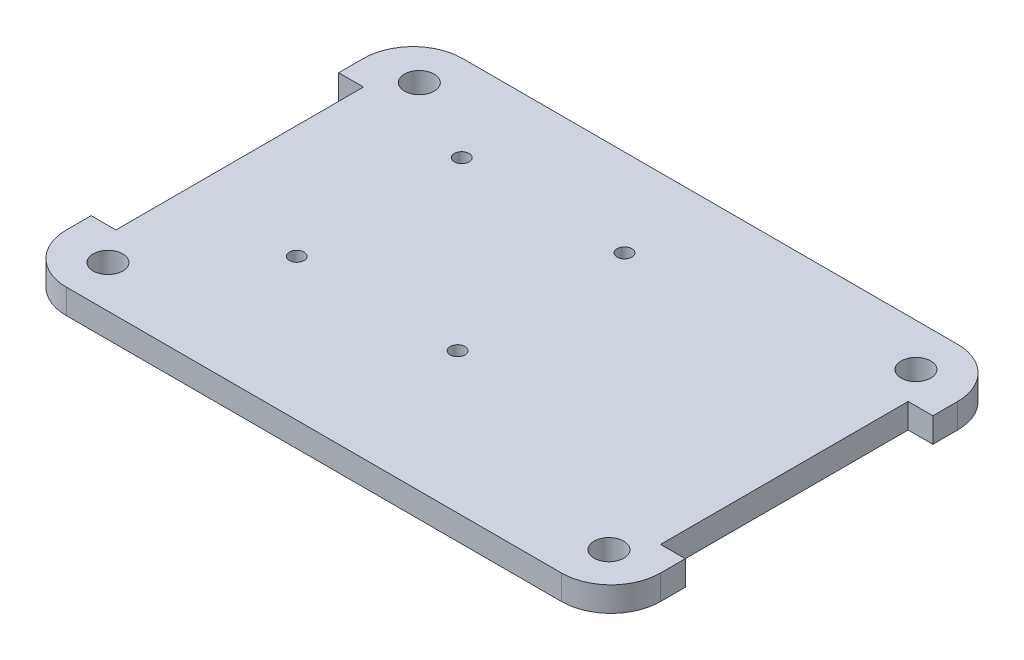
SolidWorks part; units mm, degrees
material "Acrylic (Medium-high impact)"
ref_plane "Front Plane" through (0, 0, 0) normal (0, 0, 1) x (1, 0, 0)
ref_plane "Top Plane" through (0, 0, 0) normal (0, 1, 0) x (1, 0, 0)
ref_plane "Right Plane" through (0, 0, 0) normal (1, 0, 0) x (0, 0, -1)
sketch "Sketch1" plane through (0, 0, 0) normal (0, 1, 0) x (1, 0, 0)
  line L0 (10, 0) -> (110, 0)
  line L3 (10, -80) -> (110, -80)
  line L4 (0, -10) -> (0, -15)
  line L5 (0, -70) -> (0, -65)
  line L6 (120, -10) -> (120, -15)
  line L7 (120, -70) -> (120, -65)
  line L8 (0, -15) -> (5, -15)
  line L9 (5, -15) -> (5, -65)
  line L10 (5, -65) -> (0, -65)
  line L11 (120, -15) -> (115, -15)
  line L12 (115, -15) -> (115, -65)
  line L13 (115, -65) -> (120, -65)
  arc A0 (120, -70) -> (110, -80) centre (110, -70) cw
  arc A1 (110, 0) -> (120, -10) centre (110, -10) cw
  arc A2 (0, -70) -> (10, -80) centre (10, -70) ccw
  arc A3 (10, 0) -> (0, -10) centre (10, -10) ccw
  point P15 (120, -80)
  point P18 (120, 0)
  point P21 (0, -80)
  point P24 (0, 0)
  dimension "D11" = 10
  dimension "D1" = 80
  dimension "D2" = 120
  dimension "D3" = 15
  dimension "D4" = 15
  dimension "D5" = 5
  dimension "D6" = 5
  dimension "D7" = 15
  dimension "D8" = 15
  dimension "D9" = 50
  dimension "D10" = 50
extrude "Boss-Extrude1" add sketch "Sketch1" along normal blind 5 contours L13 L7 A0 L3 A2 L5 L10 L9 L8 L4 A3 L0 A1 L6 L11 L12
sketch "Sketch2" plane through (0, 5, 0) normal (0, 1, 0) x (1, 0, 0)
  line L0 (0.189, -8.6122) -> (9.8714, -8.6088) construction
  line L1 (9.9933, -0.0789) -> (9.8714, -8.6088) construction
  line L2 (9.8868, -80.0249) -> (9.8429, -71.4949) construction
  line L3 (119.8458, -8.6842) -> (110.1658, -8.6599) construction
  line L4 (10.0313, -71.5863) -> (122.9526, -71.0617) construction
  line L5 (110.3621, -8.8959) -> (110.7556, -81.9472) construction
  circle A0 centre (9.8714, -8.5896) radius 3
  circle A1 centre (9.8798, -71.4816) radius 3.002
  circle A2 centre (110.7115, -71.1312) radius 2.9999
  circle A3 centre (110.1995, -8.6258) radius 2.9985
  dimension "D3" = 6
  dimension "D1" = 8.5299
  dimension "D2" = 9.6824
  dimension "D4" = 8.53
  dimension "D5" = 9.68
extrude "Cut-Extrude2" cut sketch "Sketch2" against normal blind 5 contours A2 | A1 | A0 | A3
sketch "Sketch14" plane through (0, 5, 0) normal (0, 1, 0) x (1, 0, 0)
  circle A0 centre (27.2787, -17.4388) radius 1.4887
  circle A1 centre (60.3712, -17.6601) radius 1.4895
  circle A2 centre (27.8724, -51.3437) radius 1.4894
  circle A3 centre (60.6283, -51.6205) radius 1.4892
extrude "Cut-Extrude3" cut sketch "Sketch14" against normal blind 5
